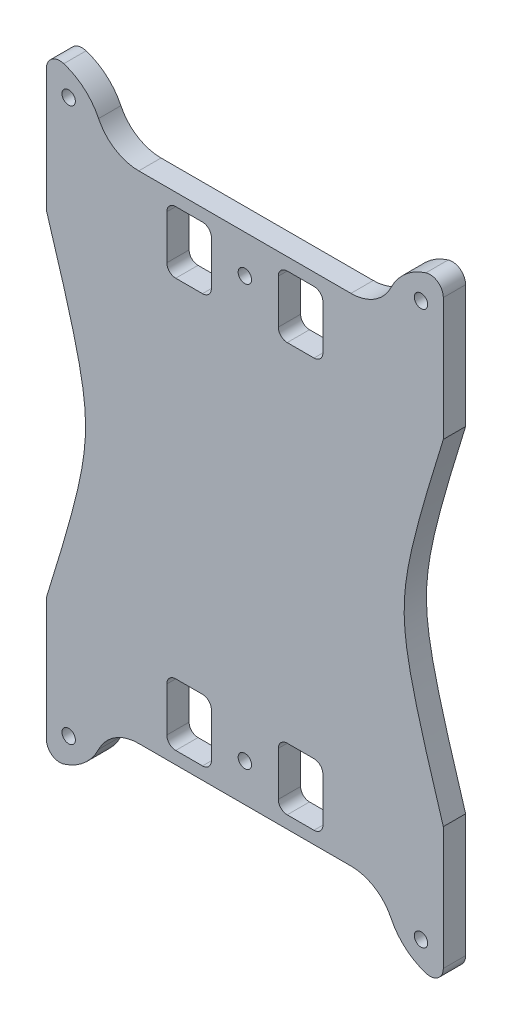
SolidWorks part; units mm, degrees
material "Acrílico (médio-alto impacto)"
ref_plane "Plano frontal" through (0, 0, 0) normal (0, 0, 1) x (1, 0, 0)
ref_plane "Plano superior" through (0, 0, 0) normal (0, 1, 0) x (1, 0, 0)
ref_plane "Plano direito" through (0, 0, 0) normal (1, 0, 0) x (0, 0, -1)
sketch "Esboço1" plane through (0, 0, 0) normal (0, 0, 1) x (1, 0, 0)
  line L0 (-8.0639, -17.8011) -> (-8.0639, -38.9203) construction
  line L1 (-31.8516, -17.8011) -> (-27.0639, -17.8011)
  line L2 (36.4361, 0.1989) -> (36.4361, -17.8011)
  line L3 (15.7238, -17.8011) -> (10.9361, -17.8011)
  line L4 (36.4361, -27.3405) -> (36.4361, -17.8011)
  line L5 (-52.5639, -27.3405) -> (-52.5639, -17.8011)
  line L6 (-52.5639, 0.1989) -> (-52.5639, -17.8011)
  line L7 (10.9361, -17.8011) -> (-27.0639, -17.8011) construction
  line L10 (36.4361, 37.7989) -> (10.9361, 37.7989) construction
  line L11 (10.9361, 93.3989) -> (-27.0639, 93.3989) construction
  line L12 (-8.0639, 93.3989) -> (-8.0639, 114.5181) construction
  line L13 (10.9361, 93.3989) -> (-27.0639, 93.3989)
  line L14 (-52.5639, 75.3989) -> (-52.5639, 93.3989)
  line L15 (-52.5639, 102.9383) -> (-52.5639, 93.3989)
  line L16 (36.4361, 102.9383) -> (36.4361, 93.3989)
  line L17 (10.9361, -17.8011) -> (-27.0639, -17.8011)
  line L18 (15.7238, 93.3989) -> (10.9361, 93.3989)
  line L19 (36.4361, 75.3989) -> (36.4361, 93.3989)
  line L20 (-31.8516, 93.3989) -> (-27.0639, 93.3989)
  arc A0 (24.7292, -23.4533) -> (32.5361, -30.2023) centre (36.4361, -17.8011) ccw
  arc A1 (24.7292, -23.4533) -> (15.7238, -17.8011) centre (15.7238, -27.8011) ccw
  arc A2 (-52.5639, -27.3405) -> (-48.6639, -30.2023) centre (-49.5639, -27.3405) ccw
  arc A3 (-40.8569, -23.4533) -> (-31.8516, -17.8011) centre (-31.8516, -27.8011) cw
  arc A4 (-40.8569, -23.4533) -> (-48.6639, -30.2023) centre (-52.5639, -17.8011) cw
  arc A5 (36.4361, -27.3405) -> (32.5361, -30.2023) centre (33.4361, -27.3405) cw
  arc A6 (36.4361, 102.9383) -> (32.5361, 105.8001) centre (33.4361, 102.9383) ccw
  arc A7 (-40.8569, 99.0511) -> (-48.6639, 105.8001) centre (-52.5639, 93.3989) ccw
  arc A8 (-40.8569, 99.0511) -> (-31.8516, 93.3989) centre (-31.8516, 103.3989) ccw
  arc A9 (-52.5639, 102.9383) -> (-48.6639, 105.8001) centre (-49.5639, 102.9383) cw
  arc A10 (24.7292, 99.0511) -> (15.7238, 93.3989) centre (15.7238, 103.3989) cw
  arc A11 (24.7292, 99.0511) -> (32.5361, 105.8001) centre (36.4361, 93.3989) cw
  conic Q0 (36.4361, 75.3989) -> (36.4361, 0.1989) control (24.7292, 37.7989) rho 0.75
  conic Q1 (-52.5639, 75.3989) -> (-52.5639, 0.1989) control (-40.8569, 37.7989) rho 0.75
  point P14 (-52.5639, -30.8011)
  point P21 (36.4361, -30.8011)
  point P45 (36.4361, 106.3989)
  point P46 (-52.5639, 106.3989)
  dimension "D1" = 26
  dimension "D2" = 20
  dimension "D8" = 13
  dimension "D9" = 3
  dimension "D11" = 10
  dimension "D3" = 25.5
  dimension "D4" = 18
  dimension "D6" = 75.2
  dimension "D10" = 9.5394
extrude "Ressalto-extrusão3" add sketch "Esboço1" along normal blind 5
sketch "Esboço3" plane through (0, 0, 0) normal (0, 0, -1) x (-1, 0, 0)
  line L1 (-4.4361, 89.2989) -> (20.5639, 89.2989)
  line L2 (-9.4361, 84.2989) -> (-9.4361, -8.7011)
  line L3 (-4.4361, -13.7011) -> (20.5639, -13.7011)
  line L4 (25.5639, 84.2989) -> (25.5639, -8.7011)
  line L5 (31.8516, -17.8011) -> (-15.7238, -17.8011) construction
  line L6 (-15.7238, 93.3989) -> (31.8516, 93.3989) construction
  line L7 (-36.4361, 75.3989) -> (-36.4361, 102.9383) construction
  line L10 (52.5639, 102.9383) -> (52.5639, 75.3989) construction
  arc A0 (20.5639, -13.7011) -> (25.5639, -8.7011) centre (20.5639, -8.7011) ccw
  arc A1 (-9.4361, -8.7011) -> (-4.4361, -13.7011) centre (-4.4361, -8.7011) ccw
  arc A2 (20.5639, 89.2989) -> (25.5639, 84.2989) centre (20.5639, 84.2989) cw
  arc A3 (-4.4361, 89.2989) -> (-9.4361, 84.2989) centre (-4.4361, 84.2989) ccw
  point P14 (-36.4361, 89.1686)
  point P17 (-9.4361, -13.7011)
  point P20 (25.5639, 89.2989)
  point P23 (-9.4361, 89.2989)
  dimension "D7" = 5
  dimension "D1" = 27
  dimension "D2" = 103
  dimension "D3" = 4.1
  dimension "D4" = 4.1
  dimension "D5" = 27
extrude "Corte-extrusão2" [suppressed] cut sketch "Esboço3" against normal blind 5
sketch "Esboço4" plane through (0, 0, 0) normal (0, 0, -1) x (-1, 0, 0)
  line L0 (-36.4361, 75.3989) -> (-36.4361, 102.9383) construction
  line L1 (52.5639, 102.9383) -> (52.5639, 75.3989) construction
  line L2 (-15.7238, 93.3989) -> (31.8516, 93.3989) construction
  line L3 (-44.641, 37.7989) -> (77.6477, 37.7989) construction
  line L4 (-7.4361, 90.5989) -> (-1.4361, 90.5989)
  line L5 (-9.4361, 88.5989) -> (-9.4361, 78.6989)
  line L6 (-7.4361, 76.6989) -> (-1.4361, 76.6989)
  line L7 (0.5639, 88.5989) -> (0.5639, 78.6989)
  line L8 (17.5639, 90.5989) -> (23.5639, 90.5989)
  line L9 (15.5639, 88.5989) -> (15.5639, 78.6989)
  line L10 (17.5639, 76.6989) -> (23.5639, 76.6989)
  line L11 (25.5639, 88.5989) -> (25.5639, 78.6989)
  line L12 (-36.4361, -27.3405) -> (-36.4361, 0.1989) construction
  line L14 (31.8516, -17.8011) -> (-15.7238, -17.8011) construction
  line L15 (25.5639, -13.0011) -> (25.5639, -3.1011)
  line L16 (17.5639, -1.1011) -> (23.5639, -1.1011)
  line L17 (15.5639, -13.0011) -> (15.5639, -3.1011)
  line L18 (17.5639, -15.0011) -> (23.5639, -15.0011)
  line L19 (0.5639, -13.0011) -> (0.5639, -3.1011)
  line L20 (-7.4361, -1.1011) -> (-1.4361, -1.1011)
  line L21 (-9.4361, -13.0011) -> (-9.4361, -3.1011)
  line L22 (-7.4361, -15.0011) -> (-1.4361, -15.0011)
  circle A0 centre (-31.4361, 99.8001) radius 1.5
  circle A1 centre (47.5639, 99.8001) radius 1.5
  circle A2 centre (8.0639, 84.8989) radius 1.5
  arc A3 (23.5639, 76.6989) -> (25.5639, 78.6989) centre (23.5639, 78.6989) ccw
  arc A4 (23.5639, 90.5989) -> (25.5639, 88.5989) centre (23.5639, 88.5989) cw
  arc A5 (17.5639, 90.5989) -> (15.5639, 88.5989) centre (17.5639, 88.5989) ccw
  arc A6 (15.5639, 78.6989) -> (17.5639, 76.6989) centre (17.5639, 78.6989) ccw
  arc A7 (-1.4361, 76.6989) -> (0.5639, 78.6989) centre (-1.4361, 78.6989) ccw
  arc A8 (-1.4361, 90.5989) -> (0.5639, 88.5989) centre (-1.4361, 88.5989) cw
  arc A9 (-7.4361, 90.5989) -> (-9.4361, 88.5989) centre (-7.4361, 88.5989) ccw
  arc A10 (-9.4361, 78.6989) -> (-7.4361, 76.6989) centre (-7.4361, 78.6989) ccw
  arc A11 (-9.4361, -3.1011) -> (-7.4361, -1.1011) centre (-7.4361, -3.1011) cw
  arc A12 (-7.4361, -15.0011) -> (-9.4361, -13.0011) centre (-7.4361, -13.0011) cw
  arc A13 (-1.4361, -15.0011) -> (0.5639, -13.0011) centre (-1.4361, -13.0011) ccw
  arc A14 (-1.4361, -1.1011) -> (0.5639, -3.1011) centre (-1.4361, -3.1011) cw
  arc A15 (15.5639, -3.1011) -> (17.5639, -1.1011) centre (17.5639, -3.1011) cw
  arc A16 (17.5639, -15.0011) -> (15.5639, -13.0011) centre (17.5639, -13.0011) cw
  arc A17 (23.5639, -15.0011) -> (25.5639, -13.0011) centre (23.5639, -13.0011) ccw
  arc A18 (23.5639, -1.1011) -> (25.5639, -3.1011) centre (23.5639, -3.1011) cw
  circle A19 centre (8.0639, -9.3011) radius 1.5
  circle A20 centre (47.5639, -24.2023) radius 1.5
  circle A21 centre (-31.4361, -24.2023) radius 1.5
  point P24 (25.5639, 76.6989)
  point P31 (15.5639, 76.6989)
  point P34 (0.5639, 76.6989)
  point P41 (-9.4361, 76.6989)
  point P46 (16.5034, 37.7989)
  point P79 (-9.4361, -1.1011)
  point P80 (0.5639, -1.1011)
  point P81 (15.5639, -1.1011)
  point P82 (25.5639, -1.1011)
  dimension "D1" = 3
  dimension "D2" = 3
  dimension "D3" = 3
  dimension "D4" = 5
  dimension "D5" = 6
  dimension "D6" = 5
  dimension "D7" = 6
  dimension "D8" = 44.5
  dimension "D9" = 8.5
  dimension "D16" = 2
  dimension "D10" = 52
  dimension "D11" = 52
  dimension "D12" = 2.8
  dimension "D13" = 2.8
  dimension "D14" = 10
  dimension "D15" = 10
  dimension "D17" = 90
  dimension "D18" = 55.6
extrude "Corte-extrusão3" cut sketch "Esboço4" against normal blind 10
